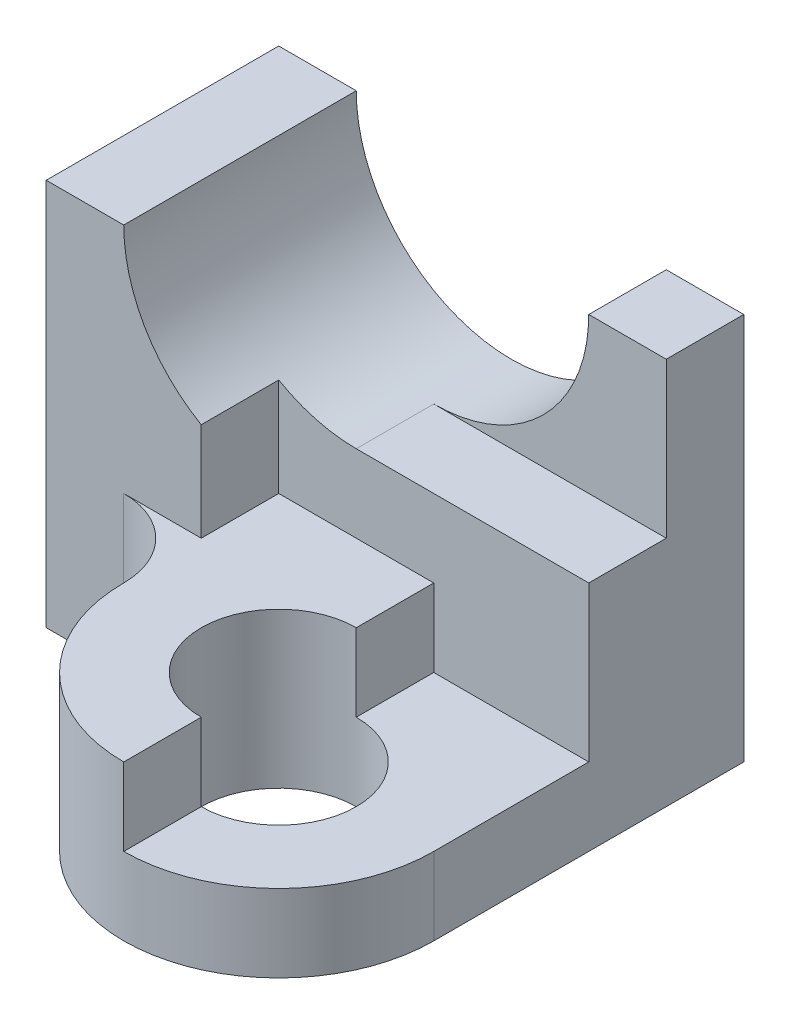
SolidWorks part; units mm, degrees
ref_plane "Front Plane" through (0, 0, 0) normal (0, 0, 1) x (1, 0, 0)
ref_plane "Top Plane" through (0, 0, 0) normal (0, 1, 0) x (1, 0, 0)
ref_plane "Right Plane" through (0, 0, 0) normal (1, 0, 0) x (0, 0, -1)
sketch "Sketch1" plane through (0, 0, 0) normal (0, 0, 1) x (1, 0, 0)
  line L0 (-2, 0) -> (-3, 0)
  line L1 (-3, 0) -> (-3, -5)
  line L2 (-3, -5) -> (3, -5)
  line L3 (3, -5) -> (3, 0)
  line L4 (3, 0) -> (2, 0)
  arc A0 (-2, 0) -> (2, 0) centre (0, 0) ccw
  dimension "D1" = 2
  dimension "D2" = 1
  dimension "D3" = 1
  dimension "D4" = 5
  dimension "D5" = 6
  dimension "D6" = 4
extrude "Boss-Extrude1" add sketch "Sketch1" along normal blind 3
sketch "Sketch2" plane through (0, 0, 0) normal (0, 1, 0) x (1, 0, 0)
  line L0 (3, -1) -> (1, -1)
  line L1 (3, -3) -> (3, 0) construction
  line L2 (1, -1) -> (1, -3)
  line L3 (1, -3) -> (3, -3)
  line L4 (3, -3) -> (3, -1)
  dimension "D1" = 1
  dimension "D2" = 2
  dimension "D3" = 2
extrude "Cut-Extrude14" cut sketch "Sketch2" against normal blind 2
sketch "Sketch6" plane through (3, 0, 0) normal (1, 0, 0) x (0, 0, -1)
  line L0 (-3, -5) -> (-2, -5)
  line L1 (-3, -5) -> (-3, -2) construction
  line L2 (-2, -5) -> (-2, -1.7321)
  line L3 (-3, -1.7321) -> (-1, -1.7321) construction
  line L4 (-2, -1.7321) -> (-3, -1.7321)
  line L5 (-3, -1.7321) -> (-3, -5)
extrude "Cut-Extrude16" cut sketch "Sketch6" against normal blind 4
sketch "Sketch8" plane through (0, 0, 2) normal (0, 0, 1) x (1, 0, 0)
  line L0 (1, -2) -> (0, -2)
  line L1 (1, -1.7321) -> (1, -2)
  arc A0 (-1, -1.7321) -> (1, -1.7321) centre (0, 0) ccw construction
  arc A1 (1, -1.7321) -> (0, -2) centre (0, 0) cw
extrude "Cut-Extrude17" cut sketch "Sketch8" against normal blind 1
sketch "Sketch9" plane through (0, -5, 0) normal (0, -1, 0) x (1, 0, 0)
  line L0 (-1, 2) -> (3, 2) construction
  line L1 (3, 2) -> (3, 4)
  line L2 (-3, 3) -> (-1, 3) construction
  line L3 (-2, 3) -> (-1, 3)
  line L4 (-1, 3) -> (-1, 2)
  line L5 (-1, 2) -> (3, 2)
  arc A0 (3, 4) -> (-1, 4) centre (1, 4) ccw
  arc A1 (-1, 4) -> (-2, 3) centre (-2, 4) cw
  circle A2 centre (1, 4) radius 1
  point P0 (1, 2)
  dimension "D3" = 2
  dimension "D5" = 2
  dimension "D1" = 2
  dimension "D2" = 2
  dimension "D4" = 4
extrude "Boss-Extrude2" add sketch "Sketch9" against normal blind 2
sketch "Sketch10" plane through (0, -3, 0) normal (0, 1, 0) x (1, 0, 0)
  line L0 (1, -2) -> (1, -6)
  line L1 (-1, -2) -> (3, -2) construction
  line L2 (1, -2) -> (3, -2)
  line L3 (3, -2) -> (3, -4)
  arc A0 (-1, -4) -> (3, -4) centre (1, -4) ccw construction
  arc A1 (1, -6) -> (3, -4) centre (1, -4) ccw
extrude "Cut-Extrude18" cut sketch "Sketch10" against normal blind 1
